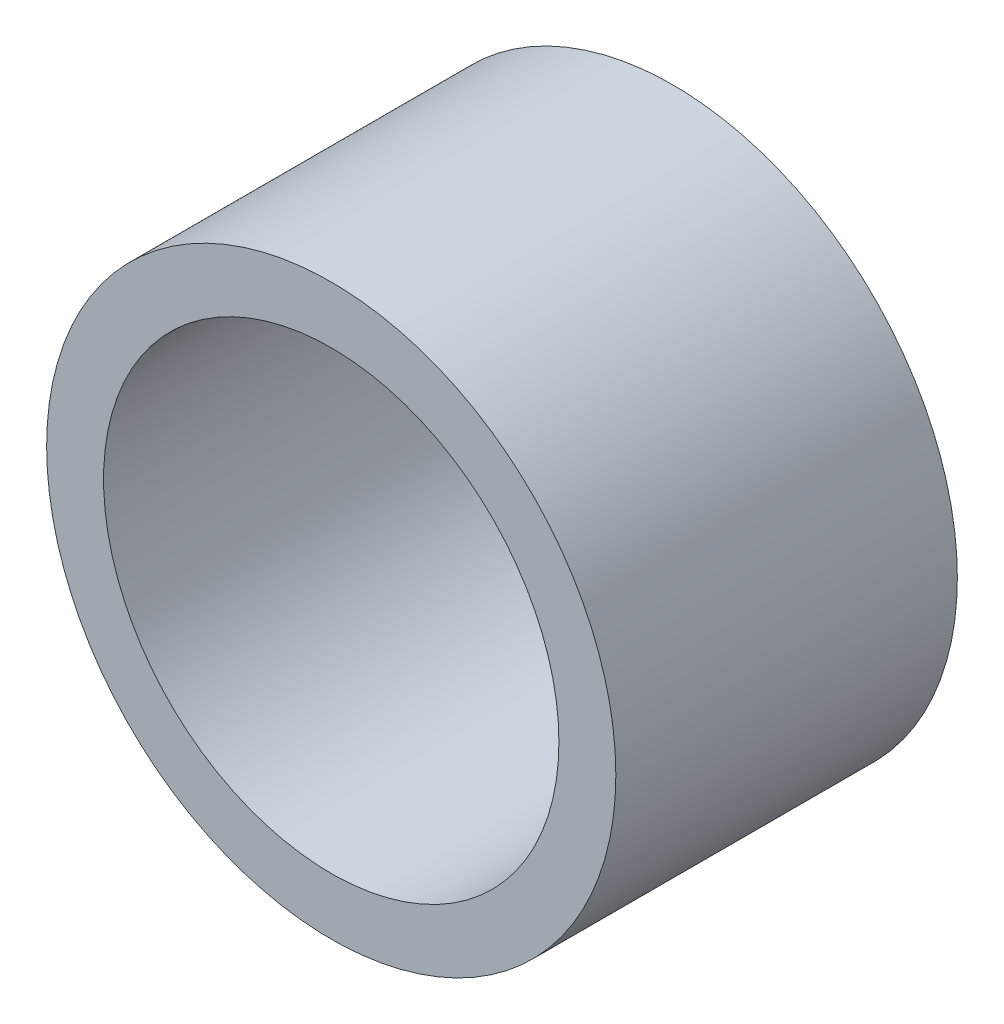
SolidWorks part; units mm, degrees
material "Phosphor bronze 10% D, UNS C52400"
ref_plane "Front Plane" through (0, 0, 0) normal (0, 0, 1) x (1, 0, 0)
ref_plane "Top Plane" through (0, 0, 0) normal (0, 1, 0) x (1, 0, 0)
ref_plane "Right Plane" through (0, 0, 0) normal (1, 0, 0) x (0, 0, -1)
sketch "Sketch1" plane through (0, 0, 0) normal (0, 0, 1) x (1, 0, 0)
  circle A0 centre (0, 0) radius 6.35
  circle A1 centre (0, 0) radius 7.9375
  dimension "D1" = 12.7
  dimension "D2" = 15.875
extrude "Boss-Extrude1" add sketch "Sketch1" along normal blind 9.525
